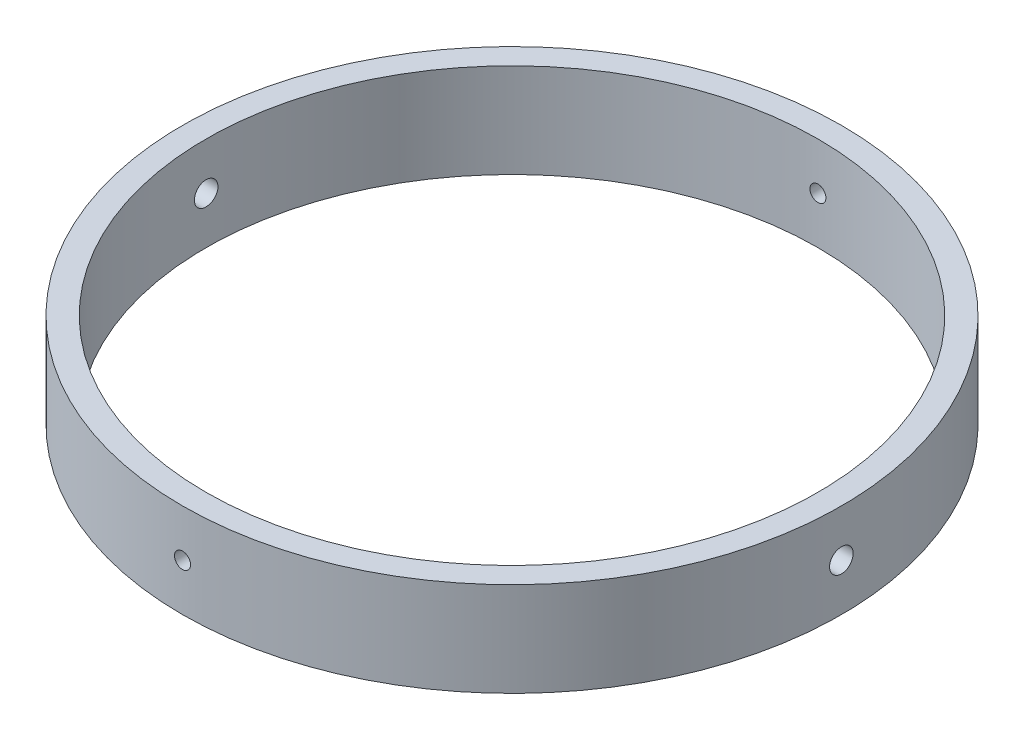
SolidWorks part; units mm, degrees
ref_plane "Front Plane" through (0, 0, 0) normal (0, 0, 1) x (1, 0, 0)
ref_plane "Top Plane" through (0, 0, 0) normal (0, 1, 0) x (1, 0, 0)
ref_plane "Right Plane" through (0, 0, 0) normal (1, 0, 0) x (0, 0, -1)
sketch "Sketch1" plane through (0, 0, 0) normal (0, 1, 0) x (1, 0, 0)
  circle A0 centre (0, 0) radius 88.9
  circle A1 centre (0, 0) radius 82.55
  dimension "D1" = 177.8
  dimension "D2" = 165.1
extrude "Boss-Extrude1" add sketch "Sketch1" along normal blind 25.4
sketch "Sketch2" plane through (0, 0, 0) normal (1, 0, 0) x (0, 0, -1)
  circle A0 centre (0, 12.7) radius 3.175
  dimension "D1" = 6.35
extrude "Cut-Extrude1" cut sketch "Sketch2" against normal through all and the other way through all
sketch "Sketch3" plane through (0, 0, 0) normal (0, 0, 1) x (1, 0, 0)
  circle A0 centre (0, 12.7) radius 2.159
  dimension "D1" = 4.318
extrude "Cut-Extrude2" cut sketch "Sketch3" against normal through all and the other way through all
